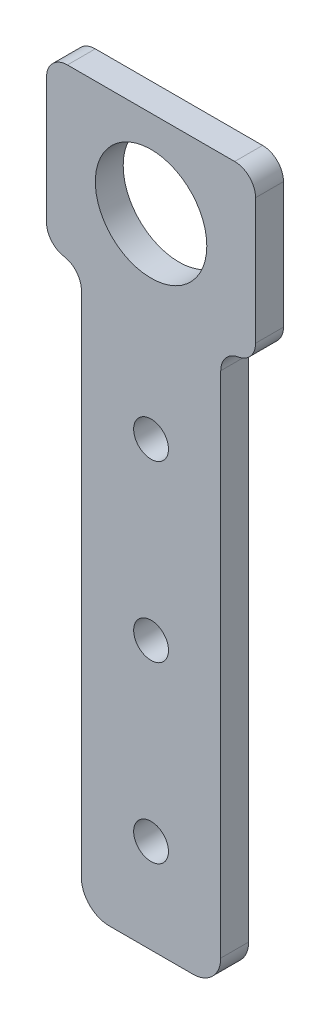
SolidWorks part; units mm, degrees
ref_plane "前视基准面" through (0, 0, 0) normal (0, 0, 1) x (1, 0, 0)
ref_plane "上视基准面" through (0, 0, 0) normal (0, 1, 0) x (1, 0, 0)
ref_plane "右视基准面" through (0, 0, 0) normal (1, 0, 0) x (0, 0, -1)
sketch "草图1" plane through (0, 0, 0) normal (0, 0, 1) x (1, 0, 0)
  line L1 (-10, -15) -> (10, -15)
  line L2 (-10, -15) -> (-10, 15)
  line L3 (-10, 15) -> (10, 15)
  line L4 (10, -15) -> (10, 15)
  line L5 (-10, -15) -> (10, 15) construction
  line L6 (-10, 15) -> (10, -15) construction
  circle A0 centre (-5, 3) radius 1.5
  circle A1 centre (5, 3) radius 1.5
  circle A2 centre (-5, -7) radius 1.5
  circle A3 centre (5, -7) radius 1.5
  point P0 (0, 0)
  dimension "D5" = 3
  dimension "D7" = 3
  dimension "D8" = 3
  dimension "D9" = 3
  dimension "D1" = 10
  dimension "D2" = 20
  dimension "D3" = 30
  dimension "D4" = 10
  dimension "D6" = 10
  dimension "D10" = 5
  dimension "D11" = 8
extrude "凸台-拉伸1" add sketch "草图1" along normal blind 4
sketch "草图2" plane through (0, 15, 0) normal (0, 1, 0) x (1, 0, 0)
  line L1 (-15, 0) -> (15, 0)
  line L2 (-15, 0) -> (-15, -4)
  line L3 (-15, -4) -> (15, -4)
  line L4 (15, 0) -> (15, -4)
  line L5 (-15, 0) -> (15, -4) construction
  line L6 (-15, -4) -> (15, 0) construction
  point P0 (0, -2)
  dimension "D1" = 30
  dimension "D2" = 0
extrude "凸台-拉伸2" add sketch "草图2" along normal blind 24
sketch "草图3" plane through (0, 0, 4) normal (0, 0, 1) x (1, 0, 0)
  line L0 (-15, 39) -> (15, 39) construction
  circle A0 centre (0, 26.5) radius 8
  dimension "D1" = 16
  dimension "D2" = 12.5
fillet "圆角1" radius 3 2 edges at (10, 15, 2) (-10, 15, 2)
extrude "切除-拉伸1" cut sketch "草图3" against normal blind 24
fillet "圆角2" radius 3 4 edges at (15, 15, 2) (15, 39, 2) (-15, 39, 2) (-15, 15, 2)
sketch "草图4" plane through (0, 0, 4) normal (0, 0, 1) x (1, 0, 0)
  circle A0 centre (5, 3) radius 1.5
  circle A1 centre (5, -7) radius 1.5
  circle A2 centre (-5, 3) radius 1.5
  circle A3 centre (-5, -7) radius 1.5
extrude "凸台-拉伸3" add sketch "草图4" against normal up to surface (4 mm away) up to face at (-8, 26.5, 0)
sketch "草图9" plane through (0, 0, 4) normal (0, 0, 1) x (1, 0, 0)
  line L0 (0, -15) -> (0, 39) construction
  line L1 (-10, -15) -> (10, -15) construction
  line L2 (-12, 39) -> (12, 39) construction
  line L3 (10, -1.5) -> (-10, -1.5) construction
  line L4 (10, -15) -> (10, 12) construction
  line L5 (-10, 12) -> (-10, -15) construction
  circle A0 centre (0, -1.5) radius 2.5
  point P12 (0, -1.5)
  dimension "D1" = 5
extrude "切除-拉伸2" cut sketch "草图9" against normal through all
sketch "草图11" plane through (0, 0, 4) normal (0, 0, 1) x (1, 0, 0)
  line L0 (10, -15) -> (10, -65)
  line L1 (10, -65) -> (-10, -65)
  line L2 (-10, -65) -> (-10, -15)
  line L3 (-10, -15) -> (10, -15)
extrude "凸台-拉伸5" add sketch "草图11" against normal up to surface (4 mm away) up to face at (2.5, -1.5, 0)
sketch "草图13" plane through (0, 0, 4) normal (0, 0, 1) x (1, 0, 0)
  line L0 (0, -1.5) -> (0, -51.5)
  line L1 (0, -51.5) -> (0, -1.5)
  line L2 (0, -1.5) -> (0, -26.5)
  circle A0 centre (0, -26.5) radius 2.5
  circle A1 centre (0, -51.5) radius 2.5
extrude "切除-拉伸3" cut sketch "草图13" against normal blind 10
fillet "圆角4" radius 4 1 edges at (10, -65, 2)
fillet "圆角5" radius 4 1 edges at (-10, -65, 2)
